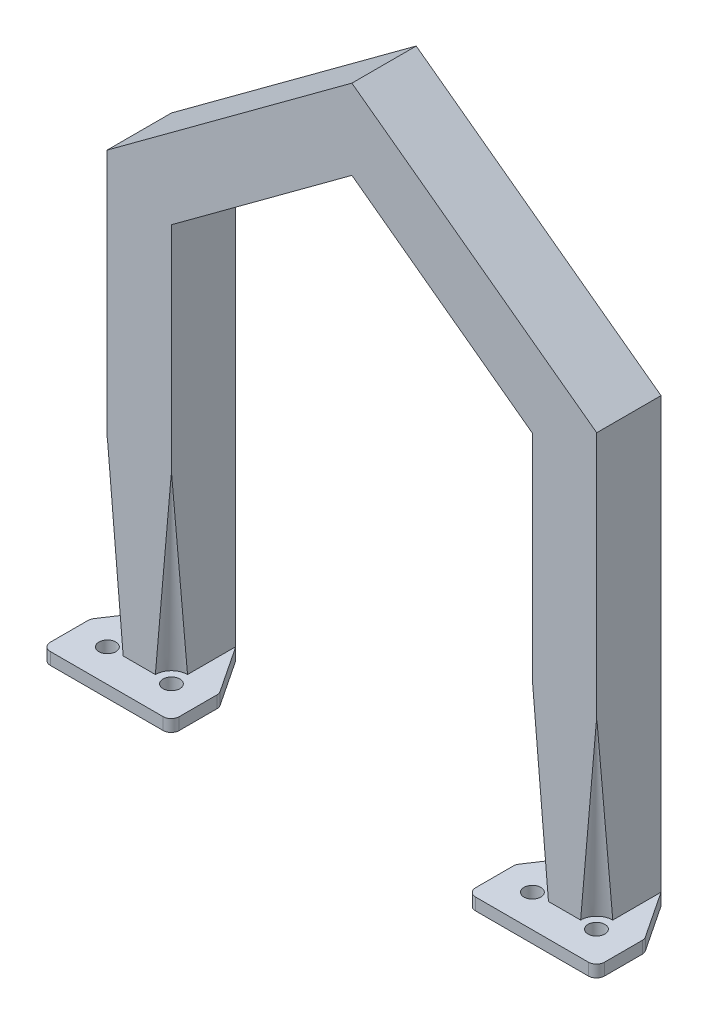
SolidWorks part; units mm, degrees
ref_plane "Front Plane" through (0, 0, 0) normal (0, 0, 1) x (1, 0, 0)
ref_plane "Top Plane" through (0, 0, 0) normal (0, 1, 0) x (1, 0, 0)
ref_plane "Right Plane" through (0, 0, 0) normal (1, 0, 0) x (0, 0, -1)
sketch "Sketch1" plane through (0, 0, 0) normal (0, 0, 1) x (1, 0, 0)
  line L0 (0, -327.8451) -> (0, 16064.408) construction
  line L1 (-60.9, 0) -> (-60.9, 107)
  line L2 (-60.9, 107) -> (0, 151.8745)
  line L3 (-60.9, 0) -> (-44.9, 0)
  line L4 (-44.9, 0) -> (-44.9, 98.9152)
  line L5 (-44.9, 98.9152) -> (0, 132)
  line L6 (44.9, 98.9152) -> (0, 132)
  line L7 (44.9, 0) -> (44.9, 98.9152)
  line L8 (60.9, 0) -> (44.9, 0)
  line L9 (60.9, 107) -> (0, 151.8745)
  line L10 (60.9, 0) -> (60.9, 107)
  line L11 (-60.9, 0) -> (-60.9, -3) construction
  line L12 (-60.9, -3) -> (-44.9, -3) construction
  line L13 (-44.9, -3) -> (-44.9, 0) construction
  line L14 (44.9, 0) -> (44.9, -3) construction
  line L15 (44.9, -3) -> (60.9, -3) construction
  line L16 (60.9, -3) -> (60.9, 0) construction
  point P10 (0, 0)
  point P17 (-52.9, 0)
  dimension "D1" = 16
  dimension "D2" = 16
  dimension "D5" = 105.8
  dimension "D7" = 3
  dimension "D3" = 110
  dimension "D4" = 135
extrude "Boss-Extrude1" add sketch "Sketch1" along normal mid plane 16
sketch "Sketch2" plane through (0, 0, 0) normal (0, -1, 0) x (1, 0, 0)
  circle A0 centre (-60.9, 8) radius 4
  circle A1 centre (-44.9, 8) radius 4
  dimension "D1" = 8
extrude "Cut-Extrude1" cut sketch "Sketch2" against normal blind 45 draft 5
sketch "Sketch3" plane through (0, 0, 0) normal (0, -1, 0) x (1, 0, 0)
  line L0 (-60.9, -8) -> (-68.937, 4.1)
  line L2 (-68.937, 4.1) -> (-68.937, 16.1)
  line L3 (-68.937, 16.1) -> (-36.863, 16.1)
  line L4 (-36.863, 16.1) -> (-36.863, 4.1)
  line L5 (-36.863, 4.1) -> (-44.9, -8)
  line L7 (-60.9, -8) -> (-44.9, -8)
  line L8 (-68.937, 4.1) -> (-36.863, 4.1) construction
  circle A0 centre (-60.837, 8) radius 2.1
  circle A1 centre (-44.9, 8) radius 2.1
  point P8 (-52.9, -8)
  point P9 (-52.9, 4.1)
  point P10 (-36.6526, 4.3671)
  dimension "D1" = 4.2
  dimension "D2" = 6
  dimension "D3" = 6
  dimension "D4" = 12
extrude "Boss-Extrude2" add sketch "Sketch3" along normal blind 3
fillet "Fillet1" radius 2 4 edges at (-36.863, -1.5, 4.1) (-36.863, -1.5, 16.1) (-68.937, -1.5, 16.1) (-68.937, -1.5, 4.1)
mirror "Mirror1" about plane through (0, 0, 0) normal (1, 0, 0) of "Fillet1", "Boss-Extrude2", "Cut-Extrude1"
equation "\"width\"= 24"
equation "\"thk\"= 3"
equation "\"holesize\"= 4.2"
equation "\"holedistance\"= ( 20 + 12 ) / 2"
equation "\"threaded_hole\"= 3.9"
equation "\"fillet_radius\"= 2"
equation "\"ground_clearance\"= 25"
equation "\"tire_thk\"= 3"
equation "\"innerwheel_diam\" = \"wheel_diam\"-2*\"tire_thk\""
equation "\"innerwheel_thk\"= 8"
equation "\"wheel_diam\"= 2*(\"width\"/2+\"ground_clearance\")"
equation "\"coloursensor_holesize\"= 2.65"
equation "\"hole_to_edge\" = 4"
equation "\"D1@Sketch1\"=\"holedistance\""
equation "\"D2@Sketch1\"=\"D1@Sketch1\""
equation "\"D1@Boss-Extrude1\"=\"holedistance\""
equation "\"D1@Sketch3\"=\"holesize\""
equation "\"D3@Sketch3\"=\"D2@Sketch3\""
equation "\"D1@Fillet1\"=\"fillet_radius\""
